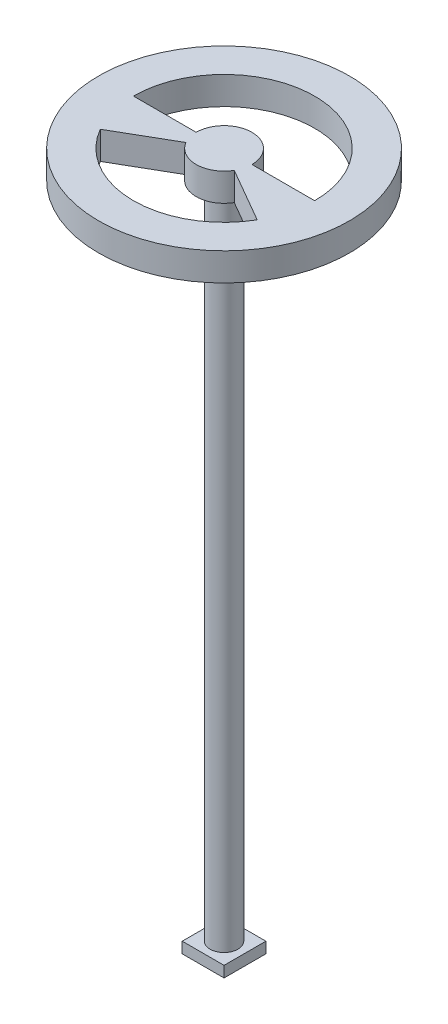
SolidWorks part; units mm, degrees
material "AISI 1020"
ref_plane "Front Plane" through (0, 0, 0) normal (0, 0, 1) x (1, 0, 0)
ref_plane "Top Plane" through (0, 0, 0) normal (0, 1, 0) x (1, 0, 0)
ref_plane "Right Plane" through (0, 0, 0) normal (1, 0, 0) x (0, 0, -1)
sketch "Sketch1" plane through (0, 0, 0) normal (0, 1, 0) x (1, 0, 0)
  line L1 (-19.05, -19.05) -> (19.05, -19.05)
  line L2 (-19.05, -19.05) -> (-19.05, 19.05)
  line L3 (-19.05, 19.05) -> (19.05, 19.05)
  line L4 (19.05, -19.05) -> (19.05, 19.05)
  line L5 (-19.05, -19.05) -> (19.05, 19.05) construction
  line L6 (-19.05, 19.05) -> (19.05, -19.05) construction
  point P0 (0, 0)
  dimension "D1" = 38.1
  dimension "D2" = 38.1
extrude "Boss-Extrude1" add sketch "Sketch1" along normal blind 10
sketch "Sketch2" plane through (0, 10, 0) normal (0, 1, 0) x (1, 0, 0)
  circle A0 centre (0, 0) radius 12.7
  dimension "D1" = 25.4
extrude "Boss-Extrude2" add sketch "Sketch2" along normal blind 600
sketch "Sketch3" plane through (0, 610, 0) normal (0, 1, 0) x (1, 0, 0)
  circle A0 centre (0, 0) radius 114.3
  dimension "D1" = 228.6
extrude "Boss-Extrude3" add sketch "Sketch3" along normal blind 25.4
sketch "Sketch5" plane through (0, 635.4, 0) normal (0, 1, 0) x (1, 0, 0)
  line L0 (82.55, 0) -> (25.4, 0)
  line L1 (0, 82.55) -> (-71.4904, 41.275) construction
  line L2 (-71.4904, 41.275) -> (-71.4904, -41.275) construction
  line L3 (-71.4904, -41.275) -> (0, -82.55) construction
  line L4 (0, -82.55) -> (71.4904, -41.275) construction
  line L5 (71.4904, -41.275) -> (71.4904, 41.275) construction
  line L6 (71.4904, 41.275) -> (0, 82.55) construction
  line L7 (-41.275, 71.4904) -> (-82.55, 0) construction
  line L8 (-82.55, 0) -> (-41.275, -71.4904) construction
  line L9 (-41.275, -71.4904) -> (41.275, -71.4904) construction
  line L10 (41.275, -71.4904) -> (82.55, 0) construction
  line L11 (82.55, 0) -> (41.275, 71.4904) construction
  line L12 (41.275, 71.4904) -> (-41.275, 71.4904) construction
  line L13 (71.4904, -41.275) -> (0, 0) construction
  line L14 (21.997, -12.7) -> (71.4904, -41.275)
  line L15 (-82.55, 0) -> (-25.4, 0)
  line L16 (-71.4904, -41.275) -> (0, 0) construction
  line L17 (-21.997, -12.7) -> (-71.4904, -41.275)
  arc A0 (-71.4904, -41.275) -> (71.4904, -41.275) centre (0, 0) ccw construction
  circle A1 centre (0, 0) radius 25.4
  circle A2 centre (0, 0) radius 71.4904 construction
  circle A3 centre (0, 0) radius 71.4904 construction
  arc A4 (-71.4904, -41.275) -> (71.4904, -41.275) centre (0, 0) ccw
  arc A5 (82.55, 0) -> (-82.55, 0) centre (0, 0) ccw construction
  arc A6 (82.55, 0) -> (-82.55, 0) centre (0, 0) ccw
  point P0 (0, 0)
  point P5 (21.997, -12.7)
  point P22 (-21.997, -12.7)
  dimension "D1" = 165.1
  dimension "D2" = 50.8
  dimension "D3" = 30
extrude "Cut-Extrude2" cut sketch "Sketch5" against normal blind 25.4 contours L0 A6 L15 A1 | L17 A4 L14 A1
